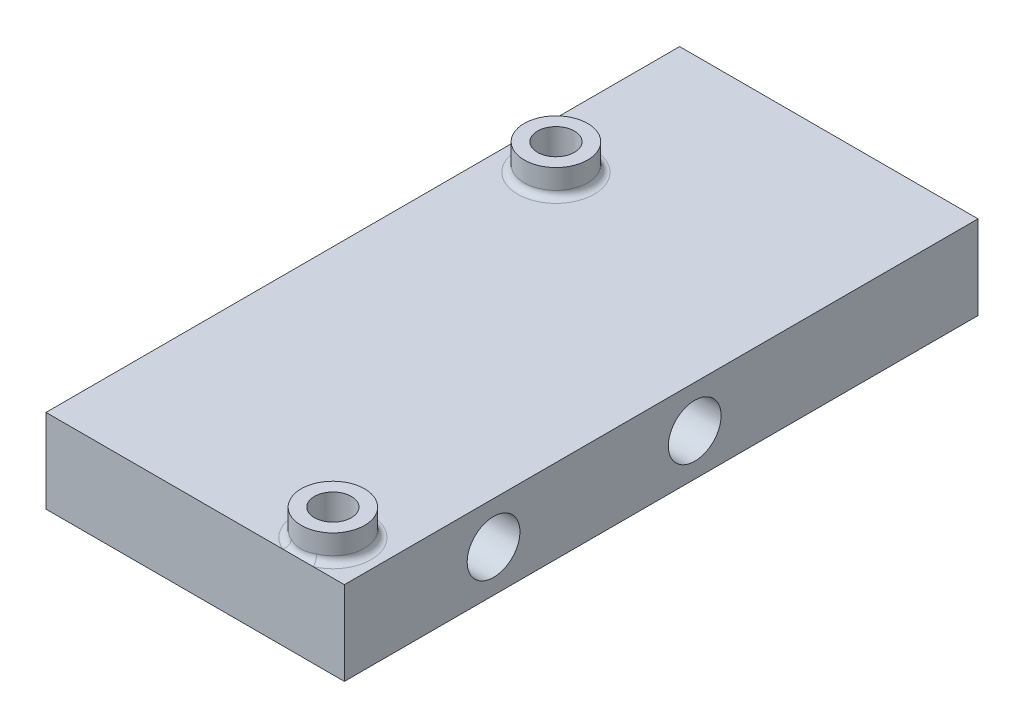
SolidWorks part; units mm, degrees
material "Nylon 12 (Density Only)"
ref_plane "Front Plane" through (0, 0, 0) normal (0, 0, 1) x (1, 0, 0)
ref_plane "Top Plane" through (0, 0, 0) normal (0, 1, 0) x (1, 0, 0)
ref_plane "Right Plane" through (0, 0, 0) normal (1, 0, 0) x (0, 0, -1)
sketch "Sketch1" plane through (0, 0, 0) normal (0, 1, 0) x (1, 0, 0)
  line L0 (0, 0) -> (22.86, 0)
  line L1 (0, 0) -> (0, 48.26)
  line L2 (22.86, 0) -> (22.86, 48.26)
  line L3 (0, 48.26) -> (22.86, 48.26)
  line L4 (0.127, 48.133) -> (22.733, 48.133)
  line L5 (22.733, 0.127) -> (22.733, 48.133)
  line L6 (0.127, 0.127) -> (22.733, 0.127)
  line L7 (0.127, 0.127) -> (0.127, 48.133)
  line L8 (11.43, 0.7937) -> (11.43, 0) construction
  line L9 (1.3335, 0.7937) -> (21.5265, 0.7938)
  line L10 (1.3335, 0.7937) -> (1.3335, 46.0058)
  line L11 (1.3335, 46.0058) -> (21.5265, 46.0058)
  line L12 (21.5265, 0.7938) -> (21.5265, 46.0058)
  line L13 (20.3073, 1.6827) -> (20.3073, 9.3231) construction
  line L14 (20.3073, 1.6827) -> (2.5835, 1.6827) construction
  line L15 (2.5835, 1.6827) -> (2.5835, 36.3058) construction
  line L16 (2.5835, 36.3058) -> (20.3073, 36.3058) construction
  line L17 (20.3073, 36.3058) -> (20.3073, 1.6827) construction
  line L18 (4.7835, 36.3058) -> (4.7835, 34.1058) construction
  line L19 (4.7835, 34.1058) -> (2.5835, 34.1058) construction
  line L21 (20.3073, 3.8827) -> (18.1073, 3.8827) construction
  line L22 (18.1073, 3.8827) -> (18.1073, 1.6827) construction
  circle A0 centre (3.6835, 35.2058) radius 1.1
  circle A1 centre (19.2073, 2.7827) radius 1.1
  circle A2 centre (3.6835, 35.2058) radius 1.4
  circle A3 centre (19.2073, 2.7827) radius 1.4
  dimension "D7" = 0.889
  dimension "D9" = 1.25
  dimension "D10" = 9.7
  dimension "D11" = 2.2
  dimension "D12" = 2.2
  dimension "D13" = 2.8
  dimension "D14" = 2.8
  dimension "D1" = 22.86
  dimension "D2" = 48.26
  dimension "D4" = 0.7937
  dimension "D5" = 20.193
  dimension "D6" = 45.212
  dimension "D8" = 1.2192
  dimension "D3" = 0.127
extrude "Boss-Extrude1" add sketch "Sketch1" along normal blind 6.35
sketch "Sketch2" plane through (0.127, 0, 0) normal (-1, 0, 0) x (0, 0, 1)
  line L0 (-48.133, 0) -> (-0.127, 6.35) construction
  line L1 (-26.67, 3.175) -> (-24.13, 3.175) construction
  line L2 (-24.13, 3.175) -> (-11.43, 3.175) construction
  circle A0 centre (-26.67, 3.175) radius 2
  circle A1 centre (-11.43, 3.175) radius 2
  point P6 (-24.13, 3.175)
  dimension "D2" = 4
  dimension "D3" = 4
  dimension "D1" = 15.24
  dimension "D4" = 12.7
extrude "Cut-Extrude1" cut sketch "Sketch2" against normal through all contours A0 | A1
sketch "Sketch3" plane through (0, 6.35, 0) normal (0, 1, 0) x (1, 0, 0)
  circle A2 centre (19.2073, 2.7827) radius 1.4
  circle A3 centre (3.6835, 35.2058) radius 1.4
  circle A4 centre (3.6835, 35.2058) radius 2.4
  circle A5 centre (19.2073, 2.7827) radius 2.4
  circle A6 centre (19.2073, 2.7827) radius 1.4 construction
  circle A7 centre (3.6835, 35.2058) radius 1.4 construction
  dimension "D1" = 1
extrude "Boss-Extrude2" add sketch "Sketch3" along normal blind 2
fillet "Fillet1" radius 0.5 2 edges at (19.2073, 6.35, -0.3827) (3.6835, 6.35, -32.8058)
